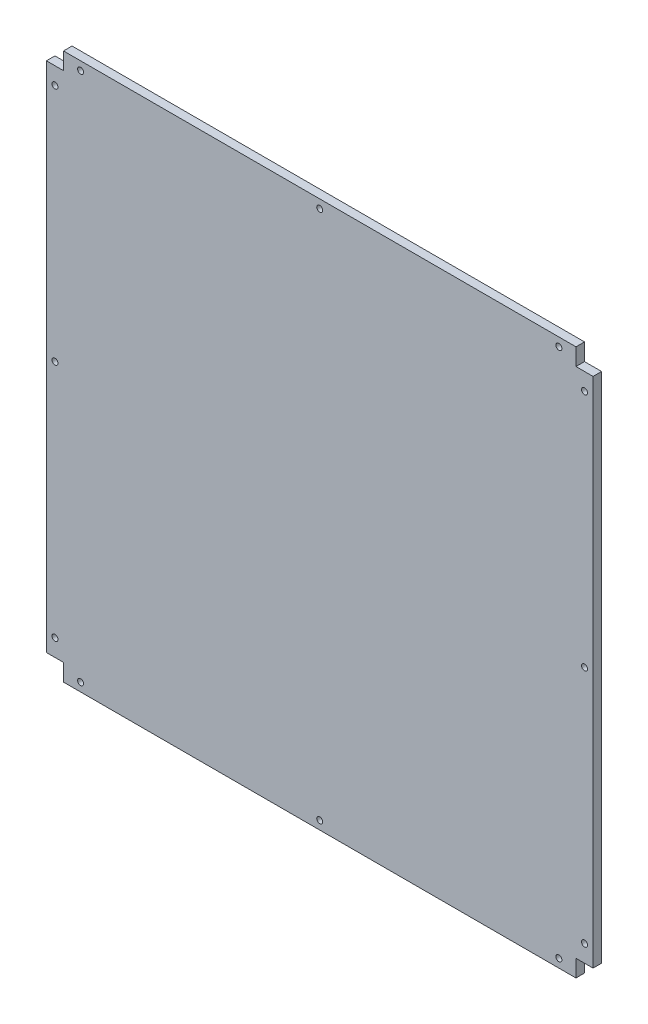
SolidWorks part; units mm, degrees
ref_plane "Front Plane" through (0, 0, 0) normal (0, 0, 1) x (1, 0, 0)
ref_plane "Top Plane" through (0, 0, 0) normal (0, 1, 0) x (1, 0, 0)
ref_plane "Right Plane" through (0, 0, 0) normal (1, 0, 0) x (0, 0, -1)
sketch "Sketch1" plane through (0, 0, 0) normal (0, 0, 1) x (1, 0, 0)
  line L0 (0, 0) -> (0, 10)
  line L1 (0, 0) -> (300, 0) construction
  line L2 (0, 0) -> (0, -300) construction
  line L3 (0, -300) -> (300, -300) construction
  line L4 (300, 0) -> (300, -300) construction
  line L5 (0, 10) -> (300, 10)
  line L6 (300, 10) -> (300, 0)
  line L7 (300, 0) -> (310, 0)
  line L8 (310, 0) -> (310, -300)
  line L9 (310, -300) -> (300, -300)
  line L10 (300, -300) -> (300, -310)
  line L11 (300, -310) -> (0, -310)
  line L12 (0, -310) -> (0, -300)
  line L13 (0, -300) -> (-10, -300)
  line L14 (-10, -300) -> (-10, 0)
  line L15 (-10, 0) -> (0, 0)
  line L16 (0, 5) -> (300, 5) construction
  line L17 (0, -150) -> (300, -150) construction
  circle A0 centre (10, 5) radius 1.75
  circle A1 centre (150, 5) radius 1.75
  circle A2 centre (290, 5) radius 1.75
  circle A3 centre (-5, -290) radius 1.75
  circle A4 centre (-5, -150) radius 1.75
  circle A5 centre (-5, -10) radius 1.75
  circle A6 centre (290, -305) radius 1.75
  circle A7 centre (150, -305) radius 1.75
  circle A8 centre (10, -305) radius 1.75
  circle A9 centre (305, -10) radius 1.75
  circle A10 centre (305, -150) radius 1.75
  circle A11 centre (305, -290) radius 1.75
  point P20 (300, 5)
  point P22 (150, -150)
  point P46 (150, -150)
  dimension "D9" = 3.5
  dimension "D10" = 3.5
  dimension "D11" = 3.5
  dimension "D1" = 300
  dimension "D2" = 300
  dimension "D3" = 10
  dimension "D4" = 10
  dimension "D5" = 10
  dimension "D6" = 10
  dimension "D7" = 10
  dimension "D8" = 10
  dimension "D12" = 4
extrude "Boss-Extrude1" add sketch "Sketch1" along normal blind 5
